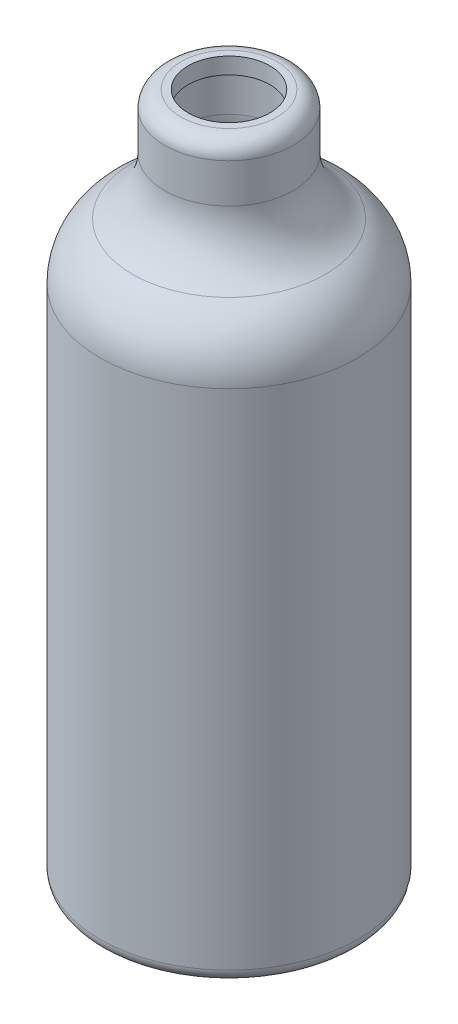
SolidWorks part; units mm, degrees
ref_plane "Front Plane" through (0, 0, 0) normal (0, 0, 1) x (1, 0, 0)
ref_plane "Top Plane" through (0, 0, 0) normal (0, 1, 0) x (1, 0, 0)
ref_plane "Right Plane" through (0, 0, 0) normal (1, 0, 0) x (0, 0, -1)
sketch "Sketch1" plane through (0, 0, 0) normal (0, 0, 1) x (1, 0, 0)
  line L0 (0, 0) -> (22.46, 0)
  line L1 (25, 2.54) -> (25, 100.3246)
  line L6 (0, 133) -> (0, 0) construction
  line L7 (0, 133) -> (9.325, 133)
  line L8 (12.5, 129.825) -> (12.5, 122.205)
  arc A3 (25, 2.54) -> (22.46, 0) centre (22.46, 2.54) cw
  arc A5 (12.5, 122.205) -> (18.75, 111.2648) centre (25.2, 122.205) ccw
  arc A6 (25, 100.3246) -> (18.75, 111.2648) centre (12.3, 100.3246) ccw
  arc A7 (12.5, 129.825) -> (9.325, 133) centre (9.325, 129.825) ccw
  point P11 (12.5, 133)
  point P15 (0, 0)
  point P16 (0, 0)
  point P17 (0, 0)
  point P18 (25, 123.4198)
  point P19 (12.5, 123.1697)
  point P20 (0, 0)
  point P21 (0, 0)
  point P22 (12.5, 101.25)
  point P23 (0, 0)
  point P24 (12.5, 123.3219)
  point P25 (18.75, 111.6156)
  dimension "D1" = 12.7
  dimension "D2" = 133
  dimension "D3" = 2.54
  dimension "D4" = 12.5
  dimension "D5" = 12.7
  dimension "D7" = 3.175
  dimension "D6" = 25
  dimension "D8" = 7.62
revolve "Revolve-Thin2" add sketch "Sketch1" angle 360 about L6
sketch "Sketch2" plane through (0, 133, 0) normal (0, 1, 0) x (1, 0, 0)
  circle A0 centre (0, 0) radius 7.9375
  dimension "D1" = 15.875
extrude "Cut-Extrude1" cut sketch "Sketch2" against normal blind 12.7
